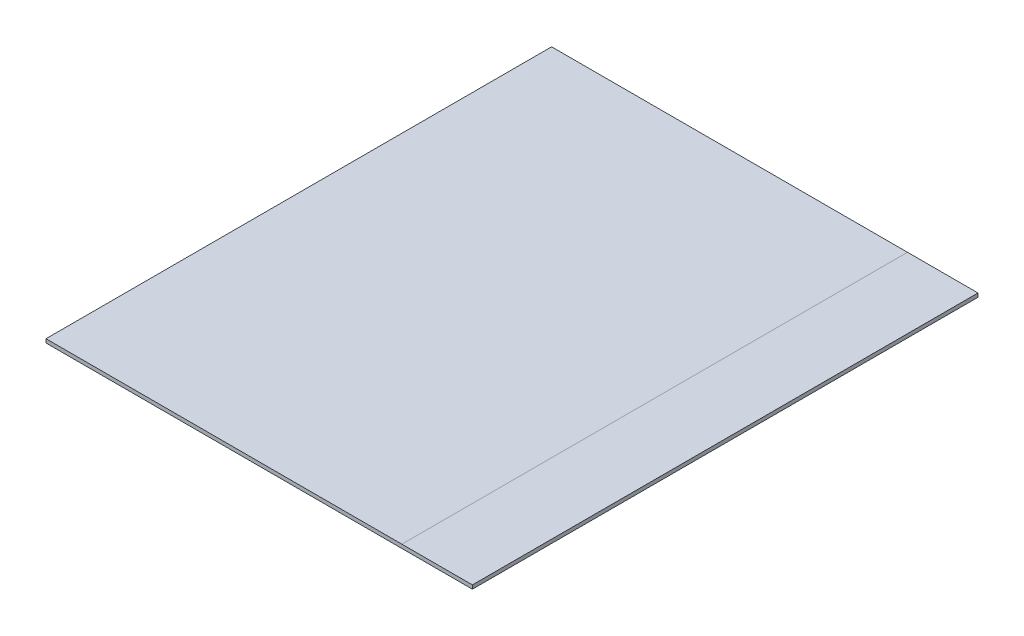
SolidWorks part; units mm, degrees
material "ABS"
ref_plane "Front Plane" through (0, 0, 0) normal (0, 0, 1) x (1, 0, 0)
ref_plane "Top Plane" through (0, 0, 0) normal (0, 1, 0) x (1, 0, 0)
ref_plane "Right Plane" through (0, 0, 0) normal (1, 0, 0) x (0, 0, -1)
sketch "Sketch1" plane through (0, 0, 0) normal (0, 1, 0) x (1, 0, 0)
  line L1 (0, 0) -> (362.8, 0)
  line L2 (0, 0) -> (0, 430.2)
  line L3 (0, 430.2) -> (362.8, 430.2)
  line L4 (362.8, 0) -> (362.8, 430.2)
  dimension "D1" = 430.2
  dimension "D2" = 362.8
extrude "Boss-Extrude1" add sketch "Sketch1" along normal blind 3.175
sketch "Sketch2" plane through (0, 3.175, 0) normal (0, 1, 0) x (1, 0, 0)
  line L0 (302.8, 430.2) -> (302.8, 0)
  line L1 (362.8, 430.2) -> (0, 430.2) construction
  line L2 (362.8, 0) -> (362.8, 430.2) construction
  dimension "D1" = 60
split line "Split Line1"
